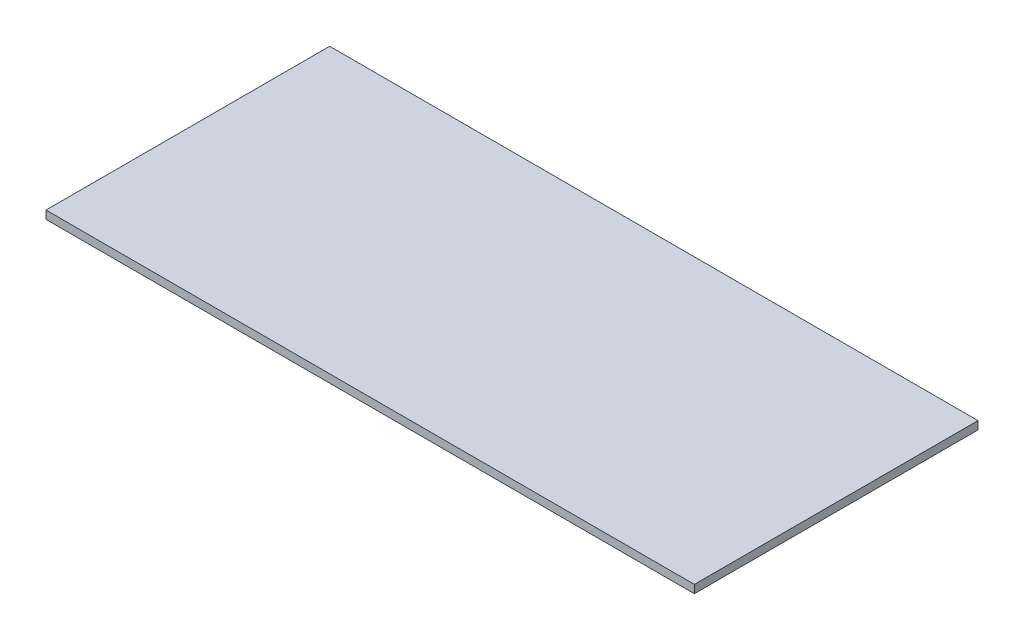
SolidWorks part; units mm, degrees
ref_plane "Front Plane" through (0, 0, 0) normal (0, 0, 1) x (1, 0, 0)
ref_plane "Top Plane" through (0, 0, 0) normal (0, 1, 0) x (1, 0, 0)
ref_plane "Right Plane" through (0, 0, 0) normal (1, 0, 0) x (0, 0, -1)
sketch "Sketch4" plane through (0, 0, 0) normal (0, 1, 0) x (1, 0, 0)
  line L1 (-80, 35) -> (80, 35)
  line L2 (-80, 35) -> (-80, -35)
  line L3 (-80, -35) -> (80, -35)
  line L4 (80, 35) -> (80, -35)
  line L5 (-80, 35) -> (80, -35) construction
  line L6 (-80, -35) -> (80, 35) construction
  point P0 (0, 0)
  dimension "D1" = 70
  dimension "160" = 160
extrude "Boss-Extrude2" add sketch "Sketch4" along normal blind 2
